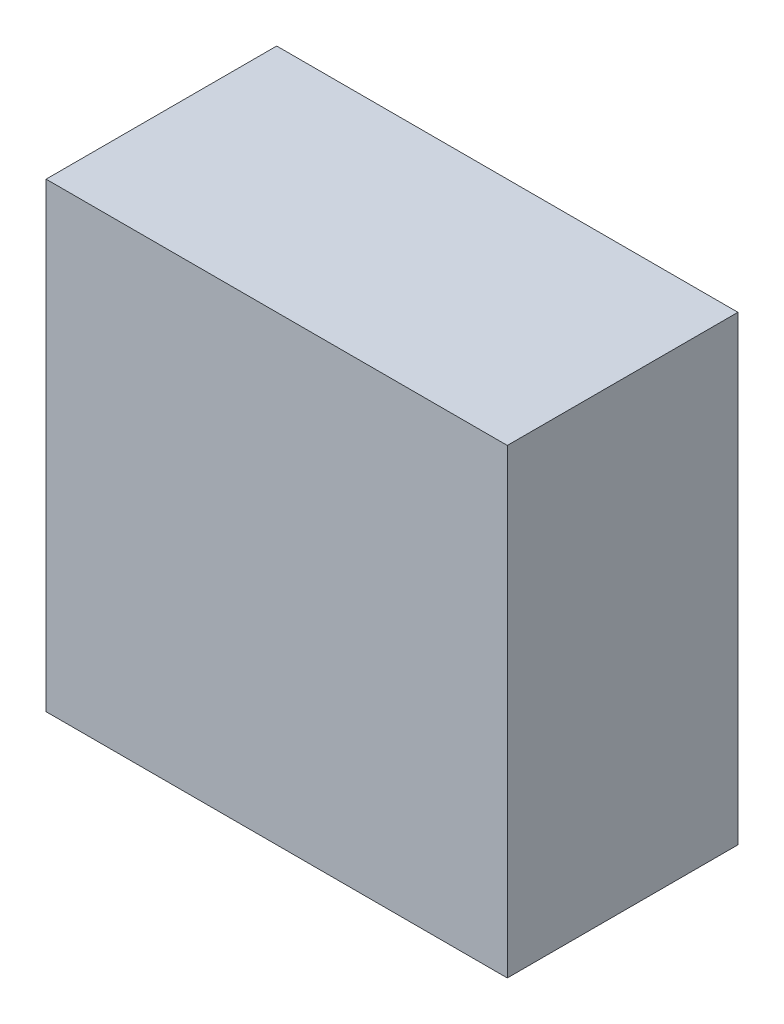
SolidWorks part; units mm, degrees
ref_plane "Plan de face" through (0, 0, 0) normal (0, 0, 1) x (1, 0, 0)
ref_plane "Plan de dessus" through (0, 0, 0) normal (0, 1, 0) x (1, 0, 0)
ref_plane "Plan de droite" through (0, 0, 0) normal (1, 0, 0) x (0, 0, -1)
sketch "Esquisse1" plane through (0, 0, 0) normal (0, 1, 0) x (1, 0, 0)
  line L1 (-200, 100) -> (200, 100)
  line L2 (-200, 100) -> (-200, -100)
  line L3 (-200, -100) -> (200, -100)
  line L4 (200, 100) -> (200, -100)
  dimension "D1" = 200
  dimension "D2" = 400
  dimension "D3" = 200
  dimension "D4" = 100
extrude "Boss.-Extru.1" add sketch "Esquisse1" along normal blind 400
